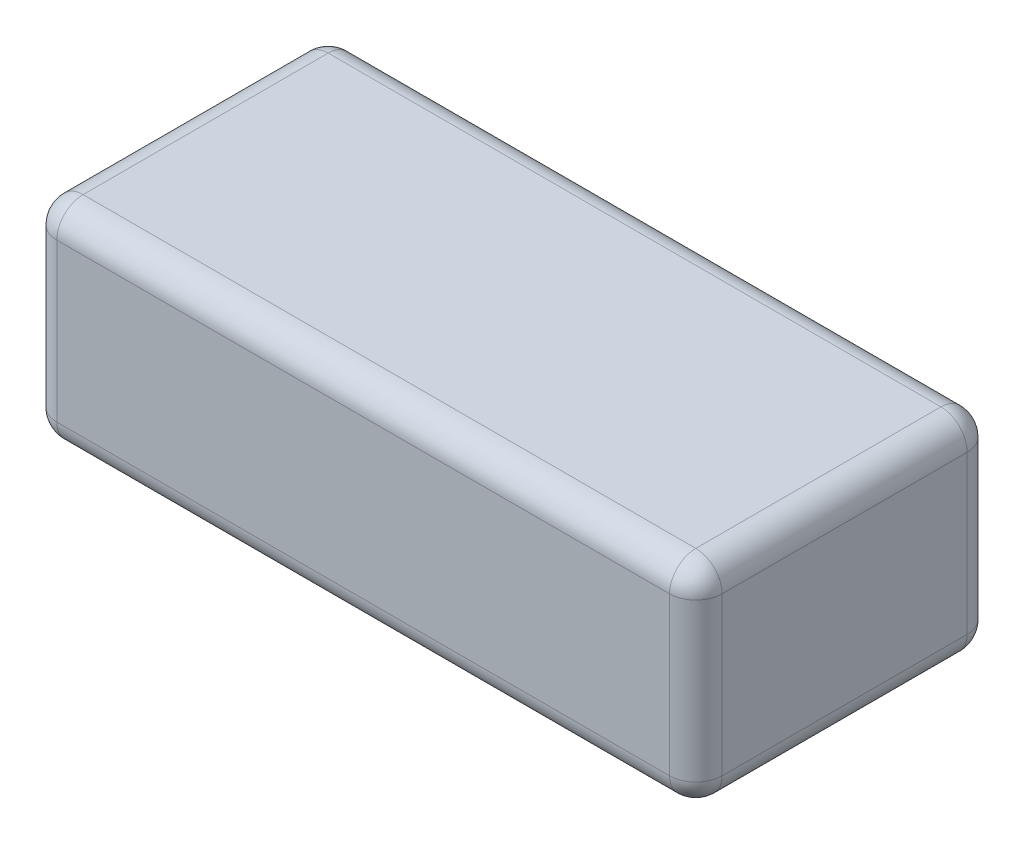
SolidWorks part; units mm, degrees
ref_plane "Front Plane" through (0, 0, 0) normal (0, 0, 1) x (1, 0, 0)
ref_plane "Top Plane" through (0, 0, 0) normal (0, 1, 0) x (1, 0, 0)
ref_plane "Right Plane" through (0, 0, 0) normal (1, 0, 0) x (0, 0, -1)
sketch "Sketch1" plane through (0, 0, 0) normal (1, 0, 0) x (0, 0, -1)
  line L1 (0, 0) -> (-34, 0)
  line L2 (0, 0) -> (0, 24)
  line L3 (0, 24) -> (-34, 24)
  line L4 (-34, 0) -> (-34, 24)
  line L5 (-17, 24) -> (-17, 0) construction
  line L6 (0, 12) -> (-34, 12) construction
  point P92 (-17, 12)
  dimension "D1" = 24
  dimension "D2" = 34
extrude "Boss-Extrude1" add sketch "Sketch1" against normal blind 76
fillet "Fillet1" radius 3 12 edges at (-38, 0, 0) (-76, 0, 17) (-38, 0, 34) (0, 0, 17) (-38, 24, 34) (-76, 24, 17) (-38, 24, 0) (0, 24, 17) (-76, 12, 0) (-76, 12, 34) (0, 12, 0) (0, 12, 34)
